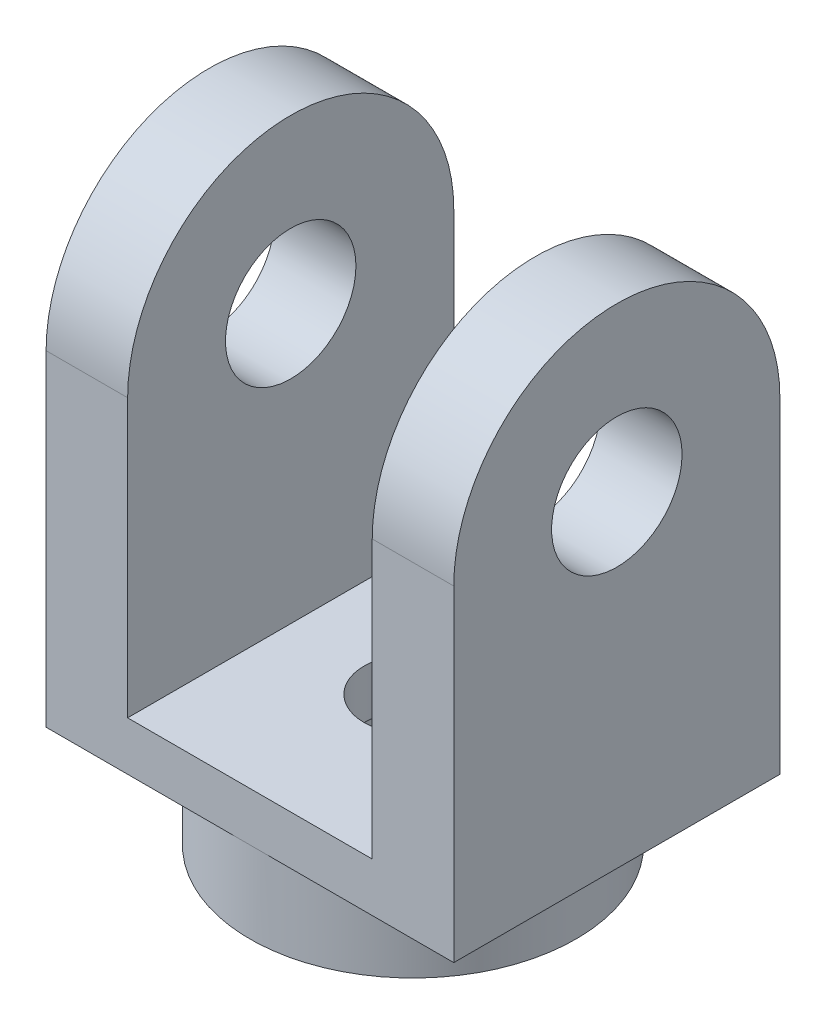
SolidWorks part; units mm, degrees
material "Plain Carbon Steel"
ref_plane "Front Plane" through (0, 0, 0) normal (0, 0, 1) x (1, 0, 0)
ref_plane "Top Plane" through (0, 0, 0) normal (0, 1, 0) x (1, 0, 0)
ref_plane "Right Plane" through (0, 0, 0) normal (1, 0, 0) x (0, 0, -1)
sketch "Sketch1" plane through (0, 0, 0) normal (0, 1, 0) x (1, 0, 0)
  line L1 (-62.5, 50) -> (62.5, 50)
  line L2 (-62.5, 50) -> (-62.5, -50)
  line L3 (-62.5, -50) -> (62.5, -50)
  line L4 (62.5, 50) -> (62.5, -50)
  line L5 (-62.5, 50) -> (62.5, -50) construction
  line L6 (-62.5, -50) -> (62.5, 50) construction
  point P0 (0, 0)
  dimension "D1" = 125
  dimension "D2" = 100
extrude "Boss-Extrude1" add sketch "Sketch1" along normal blind 15
sketch "Sketch2" plane through (0, 0, 0) normal (0, -1, 0) x (1, 0, 0)
  circle A0 centre (0, 0) radius 50
  circle A1 centre (0, 0) radius 37.5
  dimension "D1" = 100
  dimension "D2" = 75
extrude "Boss-Extrude2" add sketch "Sketch2" along normal blind 25
sketch "Sketch5" plane through (62.5, 0, 0) normal (1, 0, 0) x (0, 0, -1)
  line L0 (-50, 15) -> (-50, 100)
  line L1 (-50, 150) -> (50, 150) construction
  line L2 (50, 100) -> (50, 15)
  circle A0 centre (0, 100) radius 20
  arc A1 (-50, 100) -> (50, 100) centre (0, 100) cw
  point P10 (0, 0)
  line M7 (50, 15) -> (-50, 15)
  dimension "D2" = 40
  dimension "D1" = 135
extrude "Boss-Extrude3" add sketch "Sketch5" against normal blind 25 contours A1 L0 L2 A0 M7
mirror "Mirror1" about plane through (0, 0, 0) normal (1, 0, 0) of "Boss-Extrude3", "Boss-Extrude1"
sketch "Sketch6" plane through (0, 0, 0) normal (0, -1, 0) x (1, 0, 0)
  circle A0 centre (0, 0) radius 15
  dimension "D1" = 30
extrude "Cut-Extrude2" cut sketch "Sketch6" against normal up to surface (15 mm away) up to face at (0, 15, 0)
